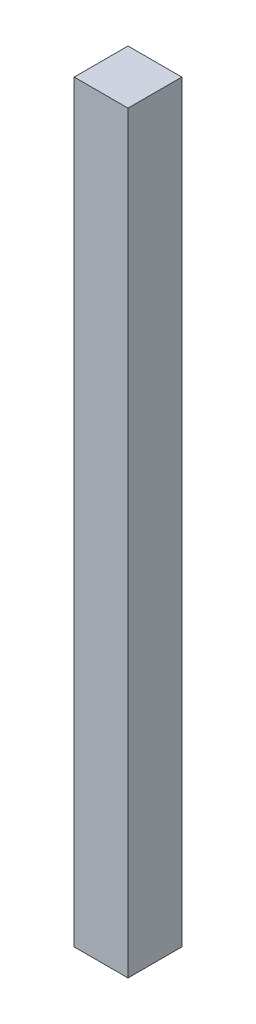
SolidWorks part; units mm, degrees
ref_plane "Front Plane" through (0, 0, 0) normal (0, 0, 1) x (1, 0, 0)
ref_plane "Top Plane" through (0, 0, 0) normal (0, 1, 0) x (1, 0, 0)
ref_plane "Right Plane" through (0, 0, 0) normal (1, 0, 0) x (0, 0, -1)
sketch "Sketch1" plane through (0, 0, 0) normal (0, 1, 0) x (1, 0, 0)
  line L1 (20, -20) -> (-20, -20)
  line L2 (20, -20) -> (20, 20)
  line L3 (20, 20) -> (-20, 20)
  line L4 (-20, -20) -> (-20, 20)
  line L5 (20, -20) -> (-20, 20) construction
  line L6 (20, 20) -> (-20, -20) construction
  point P0 (0, 0)
  dimension "D1" = 40
extrude "Boss-Extrude1" add sketch "Sketch1" along normal blind 560
